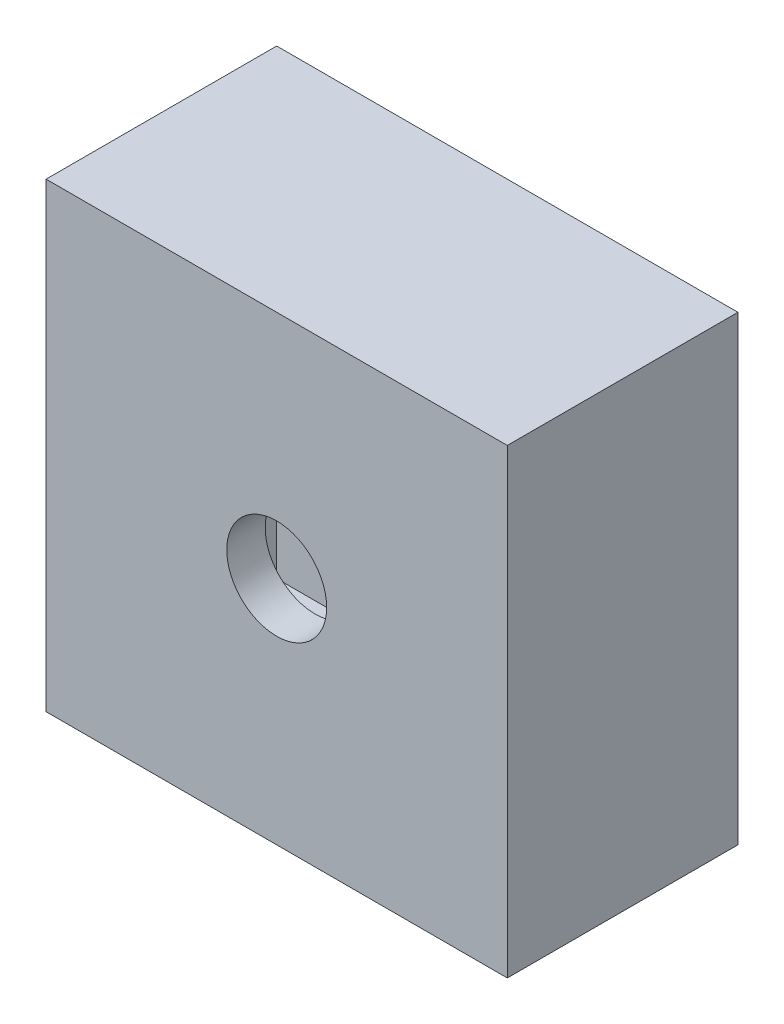
SolidWorks part; units mm, degrees
ref_plane "Front Plane" through (0, 0, 0) normal (0, 0, 1) x (1, 0, 0)
ref_plane "Top Plane" through (0, 0, 0) normal (0, 1, 0) x (1, 0, 0)
ref_plane "Right Plane" through (0, 0, 0) normal (1, 0, 0) x (0, 0, -1)
sketch "Sketch2" plane through (0, 0, 0) normal (0, 0, 1) x (1, 0, 0)
  line L1 (-600, -600) -> (600, -600)
  line L2 (-600, -600) -> (-600, 600)
  line L3 (-600, 600) -> (600, 600)
  line L4 (600, -600) -> (600, 600)
  line L5 (-600, -600) -> (600, 600) construction
  line L6 (-600, 600) -> (600, -600) construction
  point P0 (0, 0)
  dimension "D1" = 1200
extrude "Boss-Extrude1" add sketch "Sketch2" along normal blind 600
shell "Shell1" thickness 100
sketch "Sketch3" plane through (0, 0, 600) normal (0, 0, 1) x (1, 0, 0)
  line L4 (600, -600) -> (600, 600)
  line L5 (600, 600) -> (-600, 600)
  line L6 (-600, 600) -> (-600, -600)
  line L7 (-600, -600) -> (600, -600)
  line L8 (600, -600) -> (600, 600)
  line L9 (600, 600) -> (-600, 600)
  line L10 (-600, 600) -> (-600, -600)
  line L11 (-600, -600) -> (600, -600)
  dimension "D1" = 0
extrude "Boss-Extrude2" add sketch "Sketch3" against normal blind 100
sketch "Sketch4" plane through (0, 0, 0) normal (0, 0, 1) x (1, 0, 0)
  circle A0 centre (0, 0) radius 130
  dimension "D1" = 260
extrude "Cut-Extrude1" cut sketch "Sketch4" along normal through all
sketch "Sketch5" plane through (0, 0, 0) normal (0, 0, -1) x (-1, 0, 0)
  line L0 (-600, -600) -> (-600, 600) construction
  line L1 (-375, -65) -> (-245, -65)
  line L2 (-375, -65) -> (-375, 65)
  line L3 (-375, 65) -> (-245, 65)
  line L4 (-245, -65) -> (-245, 65)
  line L5 (-375, -65) -> (-245, 65) construction
  line L6 (-375, 65) -> (-245, -65) construction
  line L7 (600, -600) -> (-600, -600) construction
  point P0 (-310, 0)
  dimension "D1" = 290
  dimension "D2" = 600
  dimension "D3" = 130
extrude "Cut-Extrude2" cut sketch "Sketch5" against normal blind 150
pattern_circular "CirPattern2" count 4 over 360 about axis through (0, 0, 0) along (0, 0, 1) of "Cut-Extrude2"
